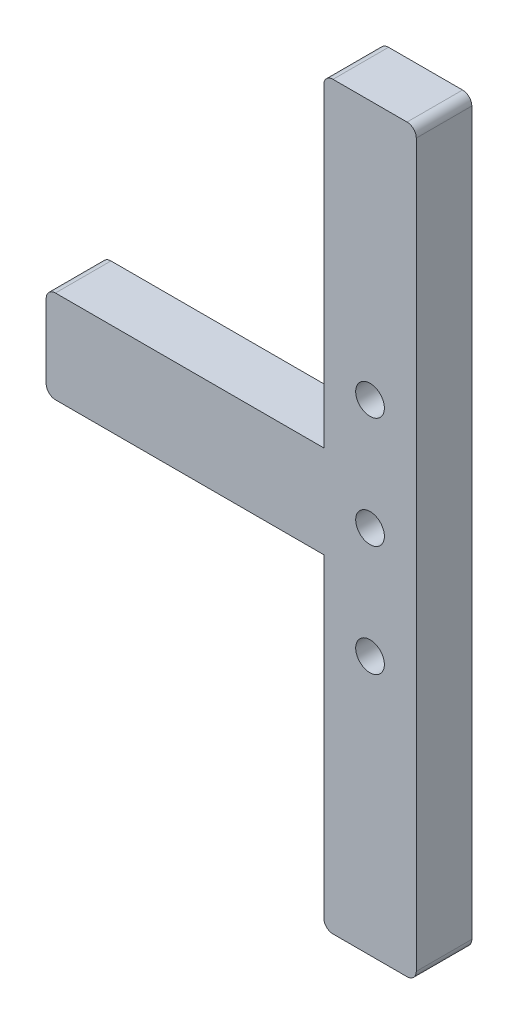
SolidWorks part; units mm, degrees
material "ABS"
ref_plane "前视基准面" through (0, 0, 0) normal (0, 0, 1) x (1, 0, 0)
ref_plane "上视基准面" through (0, 0, 0) normal (0, 1, 0) x (1, 0, 0)
ref_plane "右视基准面" through (0, 0, 0) normal (1, 0, 0) x (0, 0, -1)
other "Configuration Table"
sketch "草图1" plane through (0, 0, 0) normal (0, 0, 1) x (1, 0, 0)
  line L0 (-20, 0) -> (0, 0) construction
  line L1 (-5, 40) -> (5, 40)
  line L2 (-5, 40) -> (-5, -40)
  line L3 (-5, -40) -> (5, -40)
  line L4 (5, 40) -> (5, -40)
  line L5 (-5, 40) -> (5, -40) construction
  line L6 (-5, -40) -> (5, 40) construction
  line L7 (-5, 5) -> (-35, 5)
  line L8 (-5, 5) -> (-5, -5)
  line L9 (-5, -5) -> (-35, -5)
  line L10 (-35, 5) -> (-35, -5)
  line L11 (-5, 5) -> (-35, -5) construction
  line L12 (-5, -5) -> (-35, 5) construction
  line L13 (0, 40) -> (0, -40) construction
  circle A0 centre (0, 12) radius 1.55
  circle A1 centre (0, 0) radius 1.55
  circle A3 centre (0, -12) radius 1.55
  point P4 (0, 0)
  point P9 (-20, 0)
  point P21 (0, 0)
  dimension "D5" = 3.1
  dimension "D6" = 12
  dimension "D1" = 10
  dimension "D2" = 10
  dimension "D3" = 80
  dimension "D4" = 40
extrude "凸台-拉伸1" add sketch "草图1" along normal blind 6 contours L7 L10 L9 L2 | L4 L1 L2 L3
fillet "圆角1" radius 1 6 edges at (-5, 40, 3) (5, 40, 3) (5, -40, 3) (-5, -40, 3) (-35, -5, 3) (-35, 5, 3)
